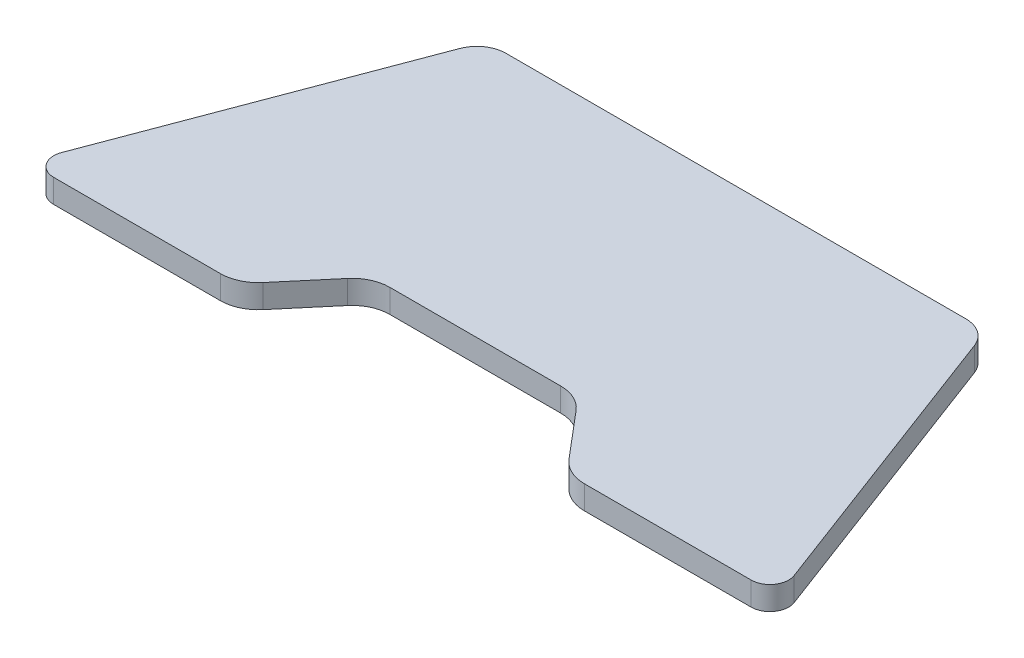
SolidWorks part; units mm, degrees
ref_plane "Front Plane" through (0, 0, 0) normal (0, 0, 1) x (1, 0, 0)
ref_plane "Top Plane" through (0, 0, 0) normal (0, 1, 0) x (1, 0, 0)
ref_plane "Right Plane" through (0, 0, 0) normal (1, 0, 0) x (0, 0, -1)
sketch "Sketch1" plane through (0, 0, 0) normal (0, 1, 0) x (1, 0, 0)
  line L5 (-48.9397, 35.5) -> (48.9397, 35.5)
  line L8 (0, 42.4113) -> (0, -63.928) construction
  line L10 (-32.5731, -32.6269) -> (-24.3042, -22.8377)
  line L16 (18.1927, -20) -> (0, -20)
  line L17 (-18.1927, -20) -> (0, -20)
  line L18 (-5.0096, 0.0045) -> (-4.9902, 0.0275)
  line L19 (32.5731, -32.6269) -> (24.3042, -22.8377)
  line L20 (74.2185, -35.5) -> (38.761, -35.5)
  line L21 (54.7697, 31.4665) -> (77.9616, -30.0897)
  line L24 (77.9616, -30.0897) -> (80, -35.5)
  line L25 (80, -35.5) -> (74.2185, -35.5)
  line L26 (-54.7697, 31.4665) -> (-77.9616, -30.0897)
  line L27 (-74.2185, -35.5) -> (-38.761, -35.5)
  line L28 (18.1927, -20) -> (0, -20)
  line L29 (32.5731, -32.6269) -> (24.3042, -22.8377)
  line L30 (74.2185, -35.5) -> (38.761, -35.5)
  line L31 (54.7697, 31.4665) -> (77.9616, -30.0897)
  arc A4 (-32.5731, -32.6269) -> (-38.761, -35.5) centre (-38.761, -27.4) cw
  arc A6 (-48.9397, 35.5) -> (-54.7697, 31.4665) centre (-48.9397, 29.27) ccw
  arc A10 (-18.1927, -20) -> (-24.3042, -22.8377) centre (-18.1927, -28) ccw
  arc A11 (18.1927, -20) -> (24.3042, -22.8377) centre (18.1927, -28) cw
  arc A12 (32.5731, -32.6269) -> (38.761, -35.5) centre (38.761, -27.4) ccw
  arc A14 (48.9397, 35.5) -> (54.7697, 31.4665) centre (48.9397, 29.27) cw
  arc A15 (-74.2185, -35.5) -> (-77.9616, -30.0897) centre (-74.2185, -31.5) cw
  arc A16 (18.1927, -20) -> (24.3042, -22.8377) centre (18.1927, -28) cw
  arc A17 (32.5731, -32.6269) -> (38.761, -35.5) centre (38.761, -27.4) ccw
  arc A18 (74.2185, -35.5) -> (77.9616, -30.0897) centre (74.2185, -31.5) ccw
  arc A19 (48.9397, 35.5) -> (54.7697, 31.4665) centre (48.9397, 29.27) cw
  point P0 (0, 0)
  point P4 (0, 0.0275)
  point P8 (-80, -35.5)
  point P9 (35, -35.5)
  point P16 (-9.0964, -20)
  point P17 (9.0964, -20)
  point P19 (-80, -35.5)
  point P23 (-35, -35.5)
  point P26 (-35, -35.5)
  point P32 (-48.25, 35.5)
  point P35 (0, 35.5)
  dimension "D3" = 160
  dimension "D4" = 4
  dimension "D8" = 48.25
  dimension "D7" = 8.1
  dimension "D9" = 6.23
  dimension "D2" = 8
  dimension "D1" = 45
extrude "Boss-Extrude1" add sketch "Sketch1" along normal blind 5
